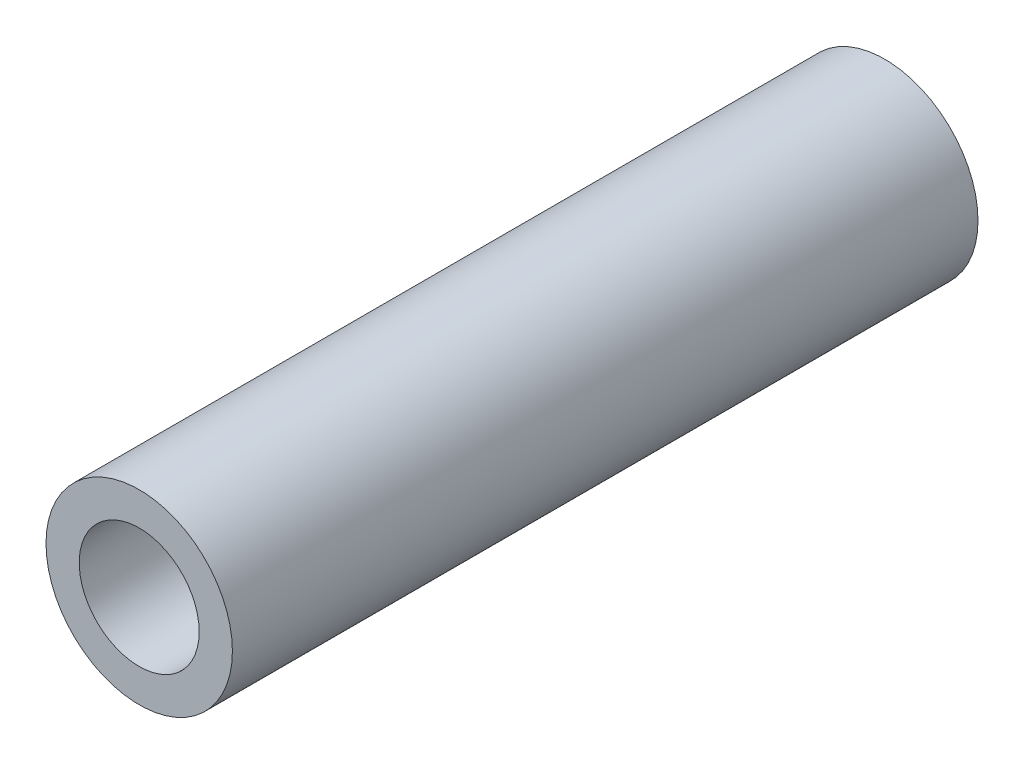
SolidWorks part; units mm, degrees
material "ABS"
ref_plane "Front Plane" through (0, 0, 0) normal (0, 0, 1) x (1, 0, 0)
ref_plane "Top Plane" through (0, 0, 0) normal (0, 1, 0) x (1, 0, 0)
ref_plane "Right Plane" through (0, 0, 0) normal (1, 0, 0) x (0, 0, -1)
sketch "Sketch1" plane through (0, 0, 0) normal (0, 0, 1) x (1, 0, 0)
  circle A0 centre (0, 0) radius 3.9688
  circle A1 centre (0, 0) radius 2.555
  dimension "D1" = 7.9375
  dimension "D2" = 5.11
extrude "Boss-Extrude1" add sketch "Sketch1" along normal blind 31.75
cosmetic thread "Cosmetic Thread1"
